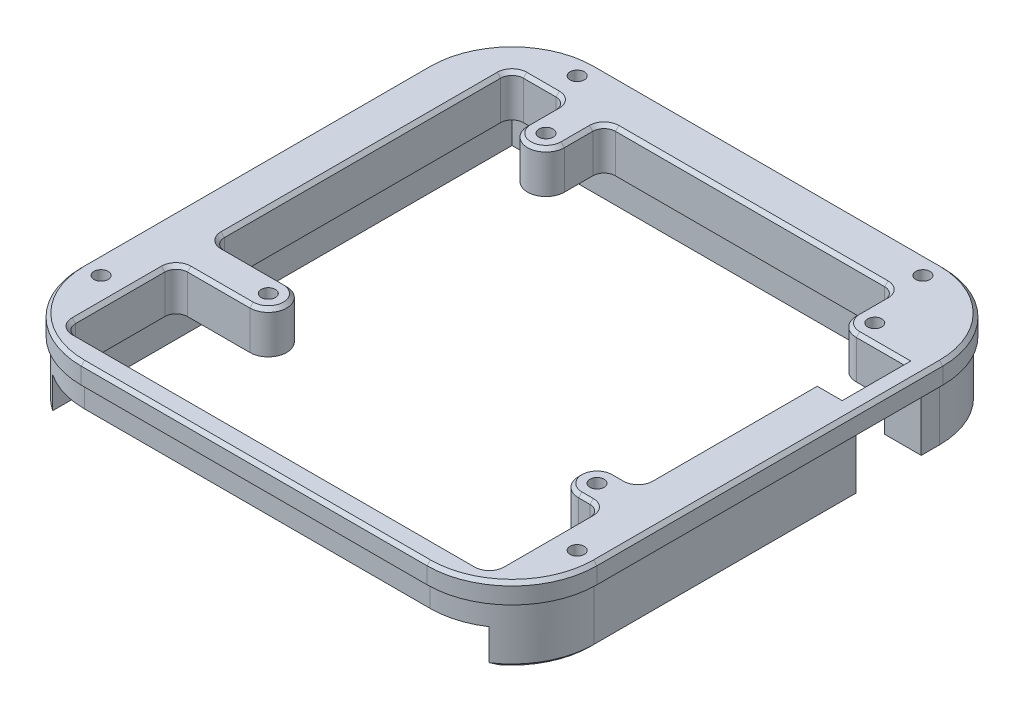
SolidWorks part; units mm, degrees
ref_plane "Front Plane" through (0, 0, 0) normal (0, 0, 1) x (1, 0, 0)
ref_plane "Top Plane" through (0, 0, 0) normal (0, 1, 0) x (1, 0, 0)
ref_plane "Right Plane" through (0, 0, 0) normal (1, 0, 0) x (0, 0, -1)
sketch "Sketch1" plane through (0, 0, 0) normal (0, 1, 0) x (1, 0, 0)
  line L0 (44.2196, 41.6627) -> (-46.7804, 41.6627)
  line L1 (-25.7804, 26.6627) -> (32.2196, 26.6627) construction
  line L2 (-25.7804, 26.6627) -> (-25.7804, -22.3373) construction
  line L3 (-25.7804, -22.3373) -> (32.2196, -22.3373) construction
  line L4 (32.2196, 26.6627) -> (32.2196, -22.3373) construction
  line L5 (36.2196, 33.6627) -> (-38.7804, 33.6627)
  line L6 (36.2196, 33.6627) -> (36.2196, -45.3373)
  line L7 (36.2196, -45.3373) -> (-38.7804, -45.3373)
  line L8 (-38.7804, 33.6627) -> (-38.7804, -45.3373)
  line L9 (-46.7804, 41.6627) -> (-46.7804, -53.3373)
  line L10 (44.2196, -53.3373) -> (-46.7804, -53.3373)
  line L11 (44.2196, 41.6627) -> (44.2196, -53.3373)
  line L12 (-22.5304, 26.6627) -> (-22.5304, 33.6627)
  line L13 (-25.7804, 23.4127) -> (-38.7804, 23.4127)
  line L14 (-25.7804, -19.0873) -> (-38.7804, -19.0873)
  line L15 (35.4696, 26.6627) -> (36.2196, 26.6627)
  line L16 (-25.7804, -25.5873) -> (-38.7804, -25.5873)
  line L17 (44.2196, -49.3373) -> (-46.7804, -49.3373)
  line L18 (-29.0304, 26.6627) -> (-29.0304, 33.6627)
  line L19 (-25.7804, 29.9127) -> (-38.7804, 29.9127)
  line L20 (32.2196, 23.4127) -> (36.2196, 23.4127)
  line L21 (32.2196, 29.9127) -> (36.2196, 29.9127)
  line L22 (28.9696, 26.6627) -> (28.9696, 33.6627)
  line L23 (32.2196, -19.0873) -> (36.2196, -19.0873)
  line L24 (32.2196, -25.5873) -> (36.2196, -25.5873)
  circle A0 centre (32.2196, 26.6627) radius 1.25
  circle A1 centre (-25.7804, 26.6627) radius 1.25
  circle A2 centre (-25.7804, -22.3373) radius 1.25
  circle A3 centre (32.2196, -22.3373) radius 1.25
  circle A4 centre (32.2196, -22.3373) radius 3.25
  circle A5 centre (-25.7804, -22.3373) radius 3.25
  circle A6 centre (-25.7804, 26.6627) radius 3.25
  circle A7 centre (32.2196, 26.6627) radius 3.25
  point P5 (-25.7804, 26.6627)
  point P6 (32.2196, 26.6627)
  point P7 (32.2196, -22.3373)
  point P8 (-25.7804, -22.3373)
  dimension "D8" = 2.5
  dimension "D9" = 2.5
  dimension "D10" = 2.5
  dimension "D11" = 2.5
  dimension "D1" = 58
  dimension "D2" = 49
  dimension "D3" = 75
  dimension "D4" = 79
  dimension "D5" = 4
  dimension "D6" = 7
  dimension "D13" = 4
  dimension "D7" = 8
  dimension "D12" = 2
extrude "Boss-Extrude1" add sketch "Sketch1" along normal blind 7.4 contours L11 L0 L9 L10 L8 L5 L6 L7 | A7 L21 L6 L5 L22 | A7 L15 L6 L21 | A6 L19 L18 | A6 L12 L5 L18 L19 | A5 L14 L8 L16 | A5 A2 | A4 A3 | A4 L24 L6 L23 | A6 A1 | A7 A0 | A7 L20 L6 L15
sketch "Sketch3" plane through (0, 0, 0) normal (0, -1, 0) x (1, 0, 0)
  line L0 (32.2196, -23.4127) -> (36.2196, -23.4127) construction
  line L1 (32.2196, -23.4127) -> (36.2196, -23.4127)
  line L2 (36.2196, -23.4127) -> (36.2196, 19.0873) construction
  line L3 (36.2196, -23.4127) -> (36.2196, 19.0873)
  line L5 (36.2196, -23.4127) -> (41.2196, -23.4127)
  line L6 (36.2196, -23.4127) -> (36.2196, -11.9127)
  line L7 (36.2196, -11.9127) -> (41.2196, -11.9127)
  line L8 (41.2196, -23.4127) -> (41.2196, -11.9127)
  dimension "D1" = 11.5
  dimension "D2" = 5
extrude "Cut-Extrude1" cut sketch "Sketch3" against normal through all contours L5 L8 L7 L3
sketch "Sketch4" plane through (0, 0, 0) normal (0, -1, 0) x (1, 0, 0)
  line L0 (-38.7804, 25.5873) -> (-38.7804, 45.3373) construction
  line L1 (36.2196, 45.3373) -> (-38.7804, 45.3373) construction
  line L2 (36.2196, -11.9127) -> (36.2196, 19.0873) construction
  line L3 (32.2196, -23.4127) -> (41.2196, -23.4127) construction
  line L4 (44.2196, -41.6627) -> (44.2196, 49.3373)
  line L5 (44.2196, 49.3373) -> (-46.7804, 49.3373)
  line L6 (-46.7804, 49.3373) -> (-46.7804, -41.6627)
  line L7 (-46.7804, -41.6627) -> (44.2196, -41.6627)
  line L8 (44.2196, -41.6627) -> (44.2196, 49.3373)
  line L10 (-46.7804, 49.3373) -> (-46.7804, -41.6627)
  line L11 (-46.7804, -41.6627) -> (44.2196, -41.6627)
  line L12 (41.2196, -23.4127) -> (41.2196, -11.9127) construction
  line L13 (28.9696, -33.6627) -> (-22.5304, -33.6627) construction
  line L14 (-38.7804, 25.5873) -> (-38.7804, 45.3373)
  line L15 (36.2196, 45.3373) -> (-38.7804, 45.3373)
  line L16 (36.2196, -11.9127) -> (36.2196, 19.0873)
  line L17 (32.2196, -23.4127) -> (41.2196, -23.4127)
  line L18 (41.2196, -23.4127) -> (41.2196, -11.9127)
  line L19 (28.9696, -33.6627) -> (-22.5304, -33.6627)
  line L20 (36.2196, -11.9127) -> (36.2196, -33.6627)
  line L21 (-39.7804, 25.5873) -> (-39.7804, 45.3373)
  line L22 (36.2196, -33.6627) -> (-38.7804, -33.6627)
  line L23 (36.2196, -33.6627) -> (36.2196, 45.3373)
  line L24 (36.2196, 45.3373) -> (-38.7804, 45.3373)
  line L25 (-38.7804, -33.6627) -> (-38.7804, 45.3373)
  line L26 (36.2196, -34.6627) -> (-39.7804, -34.6627)
  line L27 (-39.7804, -34.6627) -> (-39.7804, 45.3373)
  line L28 (36.2196, 46.3373) -> (-38.7804, 46.3373)
  line L29 (37.2196, -33.6627) -> (37.2196, 45.3373)
  line L30 (37.2196, -33.6627) -> (37.2196, -34.6627)
  line L31 (37.2196, -34.6627) -> (36.2196, -34.6627)
  line L32 (-38.7804, 46.3373) -> (-39.7804, 46.3373)
  line L33 (-39.7804, 46.3373) -> (-39.7804, 45.3373)
  line L34 (37.2196, 45.3373) -> (37.2196, 46.3373)
  line L35 (37.2196, 46.3373) -> (36.2196, 46.3373)
  line L36 (36.2196, -11.9127) -> (41.2196, -11.9127) construction
  line L37 (36.2196, -11.9127) -> (41.2196, -11.9127)
  line L42 (44.2196, 49.3373) -> (-46.7804, 49.3373)
  dimension "D1" = 0
  dimension "D2" = 1
  dimension "D3" = 1
extrude "Boss-Extrude2" add sketch "Sketch4" along normal blind 6.1
fillet "Fillet1" radius 15 4 edges at (44.2196, 0.65, -41.6627) (-46.7804, 0.65, -41.6627) (-46.7804, 0.65, 49.3373) (44.2196, 0.65, 49.3373)
sketch "Sketch8" plane through (0, -6.1, 0) normal (0, -1, 0) x (1, 0, 0)
  line L8 (29.2196, 48.7873) -> (-31.7804, 48.7873)
  line L9 (-46.2304, 34.3373) -> (-46.2304, -26.6627)
  line L10 (-31.7804, -41.1127) -> (29.2196, -41.1127)
  line L11 (43.6696, -26.6627) -> (43.6696, 34.3373)
  line L12 (29.2196, 48.7873) -> (-31.7804, 48.7873)
  line L13 (-46.2304, 34.3373) -> (-46.2304, -26.6627)
  line L14 (-31.7804, -41.1127) -> (29.2196, -41.1127)
  line L15 (43.6696, -26.6627) -> (43.6696, 34.3373)
  line L16 (29.2196, 49.3373) -> (-31.7804, 49.3373)
  line L17 (-46.7804, 34.3373) -> (-46.7804, -26.6627)
  line L18 (-31.7804, -41.6627) -> (29.2196, -41.6627)
  line L19 (44.2196, -26.6627) -> (44.2196, 34.3373)
  line L20 (29.2196, 49.3373) -> (-31.7804, 49.3373)
  line L21 (-46.7804, 34.3373) -> (-46.7804, -26.6627)
  line L22 (-31.7804, -41.6627) -> (29.2196, -41.6627)
  line L23 (44.2196, -26.6627) -> (44.2196, 34.3373)
  arc A8 (-31.7804, 48.7873) -> (-46.2304, 34.3373) centre (-31.7804, 34.3373) ccw
  arc A9 (-31.7804, 48.7873) -> (-46.2304, 34.3373) centre (-31.7804, 34.3373) ccw
  arc A10 (-46.2304, -26.6627) -> (-31.7804, -41.1127) centre (-31.7804, -26.6627) ccw
  arc A11 (-46.2304, -26.6627) -> (-31.7804, -41.1127) centre (-31.7804, -26.6627) ccw
  arc A16 (29.2196, -41.1127) -> (43.6696, -26.6627) centre (29.2196, -26.6627) ccw
  arc A17 (29.2196, -41.1127) -> (43.6696, -26.6627) centre (29.2196, -26.6627) ccw
  arc A18 (43.6696, 34.3373) -> (29.2196, 48.7873) centre (29.2196, 34.3373) ccw
  arc A19 (43.6696, 34.3373) -> (29.2196, 48.7873) centre (29.2196, 34.3373) ccw
  arc A24 (-31.7804, 49.3373) -> (-46.7804, 34.3373) centre (-31.7804, 34.3373) ccw
  arc A25 (-31.7804, 49.3373) -> (-46.7804, 34.3373) centre (-31.7804, 34.3373) ccw
  arc A26 (-46.7804, -26.6627) -> (-31.7804, -41.6627) centre (-31.7804, -26.6627) ccw
  arc A27 (-46.7804, -26.6627) -> (-31.7804, -41.6627) centre (-31.7804, -26.6627) ccw
  arc A28 (29.2196, -41.6627) -> (44.2196, -26.6627) centre (29.2196, -26.6627) ccw
  arc A29 (29.2196, -41.6627) -> (44.2196, -26.6627) centre (29.2196, -26.6627) ccw
  arc A30 (44.2196, 34.3373) -> (29.2196, 49.3373) centre (29.2196, 34.3373) ccw
  arc A31 (44.2196, 34.3373) -> (29.2196, 49.3373) centre (29.2196, 34.3373) ccw
  dimension "D1" = 0.55
  dimension "D2" = 0
extrude "Cut-Extrude2" cut sketch "Sketch8" against normal blind 10
sketch "Sketch9" plane through (43.6696, 0, 0) normal (1, 0, 0) x (0, 0, -1)
  line L0 (26.6627, 3.9) -> (-34.3373, 3.9) construction
  line L1 (26.6627, 3.9) -> (-34.3373, 3.9)
  line L4 (23.4127, -6.1) -> (23.4127, 7.4)
  line L5 (11.9127, -6.1) -> (23.4127, -6.1)
  line L6 (11.9127, 7.4) -> (11.9127, -6.1)
  line L7 (23.4127, 7.4) -> (11.9127, 7.4)
  line L8 (23.4127, -6.1) -> (23.4127, 7.4)
  line L9 (11.9127, -6.1) -> (23.4127, -6.1)
  line L10 (11.9127, 7.4) -> (11.9127, -6.1)
  line L11 (23.4127, 7.4) -> (11.9127, 7.4)
  line M5 (-34.3373, -6.1) -> (26.6627, -6.1)
  dimension "D1" = 0
extrude "Cut-Extrude3" cut sketch "Sketch9" against normal blind 10 contours L1 L10 L8 M5
sketch "Sketch10" plane through (0, -6.1, 0) normal (0, -1, 0) x (1, 0, 0)
  line L0 (37.2196, 46.3373) -> (37.2196, 46.3706)
  line L1 (-39.7804, 46.3373) -> (-39.7804, 46.3706)
  line L12 (43.6696, -26.6627) -> (43.6696, -23.4127)
  line L13 (43.6696, -23.4127) -> (37.2196, -23.4127)
  line L14 (37.2196, -23.4127) -> (37.2196, -34.6627)
  line L15 (37.2196, -34.6627) -> (-39.7804, -34.6627)
  line L16 (-39.7804, -34.6627) -> (-39.7804, 46.3373)
  line L17 (-39.7804, 46.3373) -> (37.2196, 46.3373)
  line L18 (37.2196, 46.3373) -> (37.2196, -11.9127)
  line L19 (37.2196, -11.9127) -> (43.6696, -11.9127)
  line L20 (43.6696, -11.9127) -> (43.6696, 34.3373)
  line L21 (29.2196, 48.7873) -> (-31.7804, 48.7873)
  line L22 (-46.2304, 34.3373) -> (-46.2304, -26.6627)
  line L23 (-31.7804, -41.1127) -> (29.2196, -41.1127)
  line L24 (43.6696, -26.6627) -> (43.6696, -23.4127)
  line L25 (43.6696, -23.4127) -> (37.2196, -23.4127)
  line L26 (37.2196, -23.4127) -> (37.2196, -34.6627)
  line L27 (37.2196, -34.6627) -> (-39.7804, -34.6627)
  line L28 (-39.7804, -34.6627) -> (-39.7804, 46.3373)
  line L29 (-39.7804, 46.3373) -> (37.2196, 46.3373)
  line L30 (37.2196, 46.3373) -> (37.2196, -11.9127)
  line L31 (37.2196, -11.9127) -> (43.6696, -11.9127)
  line L32 (43.6696, -11.9127) -> (43.6696, 34.3373)
  line L33 (29.2196, 48.7873) -> (-31.7804, 48.7873)
  line L34 (-46.2304, 34.3373) -> (-46.2304, -26.6627)
  line L35 (-31.7804, -41.1127) -> (29.2196, -41.1127)
  arc A4 (43.6696, 34.3373) -> (29.2196, 48.7873) centre (29.2196, 34.3373) ccw
  arc A5 (-31.7804, 48.7873) -> (-46.2304, 34.3373) centre (-31.7804, 34.3373) ccw
  arc A6 (-46.2304, -26.6627) -> (-31.7804, -41.1127) centre (-31.7804, -26.6627) ccw
  arc A7 (29.2196, -41.1127) -> (43.6696, -26.6627) centre (29.2196, -26.6627) ccw
  arc A8 (43.6696, 34.3373) -> (29.2196, 48.7873) centre (29.2196, 34.3373) ccw
  arc A9 (-31.7804, 48.7873) -> (-46.2304, 34.3373) centre (-31.7804, 34.3373) ccw
  arc A10 (-46.2304, -26.6627) -> (-31.7804, -41.1127) centre (-31.7804, -26.6627) ccw
  arc A11 (29.2196, -41.1127) -> (43.6696, -26.6627) centre (29.2196, -26.6627) ccw
  line M22 (-39.7804, 46.3373) -> (37.2196, 46.3373)
  arc M26 (43.6696, 34.3373) -> (29.2196, 48.7873) centre (29.2196, 34.3373) ccw
  line M27 (29.2196, 48.7873) -> (-31.7804, 48.7873)
  arc M28 (-31.7804, 48.7873) -> (-46.2304, 34.3373) centre (-31.7804, 34.3373) ccw
  dimension "D1" = 0
extrude "Cut-Extrude4" cut sketch "Sketch10" against normal up to surface (6.1 mm away) contours L1 L0 M22 M26 M27 M28 up to face at (2.3327, 0, 0.4542)
fillet "Fillet2" radius 2 10 edges at (-38.7804, 3.7, 19.0873) (-38.7804, 3.7, 25.5873) (36.2196, 3.7, 25.5873) (36.2196, 3.7, 19.0873) (-38.7804, 3.7, -33.6627) (-29.0304, 3.7, -33.6627) (-22.5304, 3.7, -33.6627) (28.9696, 3.7, -33.6627) (-38.7804, 3.7, 45.3373) (36.2196, 3.7, 45.3373)
sketch "Sketch11" plane through (0, 7.4, 0) normal (0, 1, 0) x (1, 0, 0)
  line L0 (-39.7804, 34.6627) -> (-39.7804, -46.3706) construction
  line L1 (37.2196, 11.9127) -> (37.2196, -46.3706) construction
  line L2 (37.2196, 34.6627) -> (37.2196, 23.4127) construction
  line L3 (37.2196, 34.6627) -> (-39.7804, 34.6627) construction
  line L4 (-46.7804, 26.6627) -> (-46.7804, -34.3373)
  line L5 (-31.7804, -49.3373) -> (29.2196, -49.3373)
  line L6 (44.2196, -34.3373) -> (44.2196, 26.6627)
  line L7 (29.2196, 41.6627) -> (-31.7804, 41.6627)
  line L8 (-46.7804, 26.6627) -> (-46.7804, -34.3373)
  line L9 (-31.7804, -49.3373) -> (29.2196, -49.3373)
  line L10 (44.2196, -34.3373) -> (44.2196, 26.6627)
  line L11 (29.2196, 41.6627) -> (-31.7804, 41.6627)
  line L12 (-39.7804, 34.6627) -> (-39.7804, -46.3706)
  line L13 (37.2196, 11.9127) -> (37.2196, -46.3706)
  line L14 (37.2196, 34.6627) -> (37.2196, 23.4127)
  line L15 (37.2196, 34.6627) -> (-39.7804, 34.6627)
  line L16 (-31.7804, 41.6627) -> (-31.7804, 34.6627) construction
  line L17 (29.2196, 41.6627) -> (29.2196, 34.6627) construction
  line L18 (-46.7804, -34.3373) -> (-39.7804, -34.3373) construction
  line L19 (44.2196, -34.3373) -> (37.2196, -34.3373) construction
  arc A4 (-46.7804, -34.3373) -> (-31.7804, -49.3373) centre (-31.7804, -34.3373) ccw
  arc A5 (29.2196, -49.3373) -> (44.2196, -34.3373) centre (29.2196, -34.3373) ccw
  arc A6 (44.2196, 26.6627) -> (29.2196, 41.6627) centre (29.2196, 26.6627) ccw
  arc A7 (-31.7804, 41.6627) -> (-46.7804, 26.6627) centre (-31.7804, 26.6627) ccw
  arc A8 (-46.7804, -34.3373) -> (-31.7804, -49.3373) centre (-31.7804, -34.3373) ccw
  arc A9 (29.2196, -49.3373) -> (44.2196, -34.3373) centre (29.2196, -34.3373) ccw
  arc A10 (44.2196, 26.6627) -> (29.2196, 41.6627) centre (29.2196, 26.6627) ccw
  arc A11 (-31.7804, 41.6627) -> (-46.7804, 26.6627) centre (-31.7804, 26.6627) ccw
  point P19 (-31.7804, 38.1627)
  point P23 (29.2196, 38.1627)
  point P24 (40.7196, -34.3373)
  point P25 (-43.2804, -34.3373)
  dimension "D1" = 0
hole_wizard "Tap Drill for M3x0.5 Tap1" positions "3DSketch2" profile "Sketch12" hole size "M3x0.5" standard "ANSI Metric" end condition through all
sketch3d "3DSketch2"
  point P0 (-31.7804, 7.4, -38.1627)
  point P3 (29.2196, 7.4, -38.1627)
  point P6 (-43.2804, 7.4, 34.3373)
  point P9 (40.7196, 7.4, 34.3373)
sketch "Sketch12" plane through (-31.7804, 7.4, -38.1627) normal (1, 0, 0) x (0, 0, 1)
  line L0 (0, 0) -> (0, 13.5)
  line L1 (0, 13.5) -> (1.25, 13.5)
  line L2 (1.25, 13.5) -> (1.25, 0)
  line L5 (1.25, 0) -> (0, 0)
  line L11 (0, -6.35) -> (0, 107.95) construction
  dimension "Thru Hole Dia." = 2.5
  dimension "Thru Hole Depth" = 13.5
chamfer "Chamfer1" distance 0.6 angle 45 51 edges at (-39.7804, -6.1, 5.854) (-1.2804, -6.1, -34.6627) (37.2196, -6.1, -29.0377) (40.4446, -6.1, -23.4127) (41.9554, -6.1, 41.1638) (43.6696, -6.1, 11.2123) (40.4446, -6.1, -11.9127) (37.2196, -6.1, 17.229) (43.6696, -6.1, -25.0377) (-44.5162, -6.1, 41.1638) (39.4373, -6.1, -36.8804) (-46.2304, -6.1, 3.8373) (-1.2804, -6.1, -41.1127) (-41.9981, -6.1, -36.8804) (-1.2804, 7.4, 49.3373) (39.8262, 7.4, 44.9439) (-42.387, 7.4, 44.9439) (44.2196, 7.4, 3.8373) (-46.7804, 7.4, 3.8373) (39.8262, 7.4, -37.2693) (-42.387, 7.4, -37.2693) (-1.2804, 7.4, -41.6627) (36.2196, 7.4, 2.5873) (35.6338, 7.4, 18.5015) (33.2196, 7.4, 19.0873) (28.9696, 7.4, 22.3373) (33.2196, 7.4, 25.5873) (35.6338, 7.4, 26.173) (36.2196, 7.4, 35.4623) (35.6338, 7.4, 44.7515) (-1.2804, 7.4, 45.3373) (-38.1946, 7.4, 44.7515) (-38.7804, 7.4, 35.4623) (-38.1946, 7.4, 26.173) (-31.2804, 7.4, 25.5873) (-22.5304, 7.4, 22.3373) (-31.2804, 7.4, 19.0873) (-38.1946, 7.4, 18.5015) (-38.7804, 7.4, -7.2877) (-38.1946, 7.4, -33.077) (-33.9054, 7.4, -33.6627) (-29.6162, 7.4, -33.077) (36.7196, 7.4, -23.4127) (-29.0304, 7.4, -29.1627) (29.9215, 7.4, -24.3646) (-25.7804, 7.4, -23.4127) (28.9696, 7.4, -29.1627) (-22.5304, 7.4, -29.1627) (28.3838, 7.4, -33.077) (-21.9446, 7.4, -33.077) (3.2196, 7.4, -33.6627)
sketch "Sketch13" plane through (0, 7.4, 0) normal (0, 1, 0) x (1, 0, 0)
  line L0 (29.2196, 41.6627) -> (-31.7804, 41.6627) construction
  line L1 (-46.7804, 26.6627) -> (-46.7804, -34.3373) construction
  line L2 (-31.7804, -49.3373) -> (29.2196, -49.3373) construction
  line L3 (44.2196, -34.3373) -> (44.2196, 26.6627) construction
  line L4 (29.2196, 41.6627) -> (-31.7804, 41.6627)
  line L5 (-46.7804, 26.6627) -> (-46.7804, -34.3373)
  line L6 (-31.7804, -49.3373) -> (29.2196, -49.3373)
  line L7 (44.2196, -34.3373) -> (44.2196, 26.6627)
  line L8 (29.2196, 34.2627) -> (-31.7804, 34.2627)
  line L9 (-39.3804, 26.6627) -> (-39.3804, -34.3373)
  line L10 (-31.7804, -41.9373) -> (29.2196, -41.9373)
  line L11 (36.8196, -34.3373) -> (36.8196, 26.6627)
  circle A0 centre (-43.2804, -34.3373) radius 1.25 construction
  circle A1 centre (40.7196, -34.3373) radius 1.25 construction
  circle A2 centre (29.2196, 38.1627) radius 1.25 construction
  circle A3 centre (-31.7804, 38.1627) radius 1.25 construction
  arc A4 (-31.7804, 41.6627) -> (-46.7804, 26.6627) centre (-31.7804, 26.6627) ccw construction
  arc A5 (-46.7804, -34.3373) -> (-31.7804, -49.3373) centre (-31.7804, -34.3373) ccw construction
  arc A6 (29.2196, -49.3373) -> (44.2196, -34.3373) centre (29.2196, -34.3373) ccw construction
  arc A7 (44.2196, 26.6627) -> (29.2196, 41.6627) centre (29.2196, 26.6627) ccw construction
  circle A8 centre (-43.2804, -34.3373) radius 1.25
  circle A9 centre (40.7196, -34.3373) radius 1.25
  circle A10 centre (29.2196, 38.1627) radius 1.25
  circle A11 centre (-31.7804, 38.1627) radius 1.25
  arc A12 (-31.7804, 41.6627) -> (-46.7804, 26.6627) centre (-31.7804, 26.6627) ccw
  arc A13 (-46.7804, -34.3373) -> (-31.7804, -49.3373) centre (-31.7804, -34.3373) ccw
  arc A14 (29.2196, -49.3373) -> (44.2196, -34.3373) centre (29.2196, -34.3373) ccw
  arc A15 (44.2196, 26.6627) -> (29.2196, 41.6627) centre (29.2196, 26.6627) ccw
  arc A16 (-31.7804, 34.2627) -> (-39.3804, 26.6627) centre (-31.7804, 26.6627) ccw
  arc A17 (-39.3804, -34.3373) -> (-31.7804, -41.9373) centre (-31.7804, -34.3373) ccw
  arc A18 (29.2196, -41.9373) -> (36.8196, -34.3373) centre (29.2196, -34.3373) ccw
  arc A19 (36.8196, 26.6627) -> (29.2196, 34.2627) centre (29.2196, 26.6627) ccw
  dimension "D1" = 7.4
